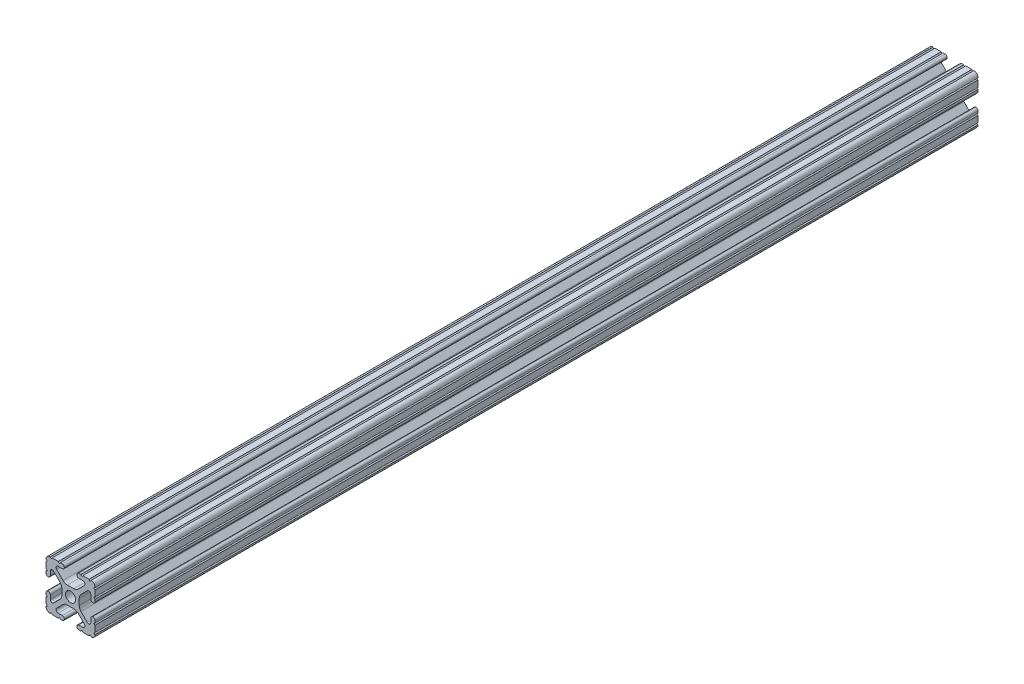
SolidWorks part; units mm, degrees
ref_plane "Front Plane" through (0, 0, 0) normal (0, 0, 1) x (1, 0, 0)
ref_plane "Top Plane" through (0, 0, 0) normal (0, 1, 0) x (1, 0, 0)
ref_plane "Right Plane" through (0, 0, 0) normal (1, 0, 0) x (0, 0, -1)
sketch "Sketch1" plane through (0, 0, 0) normal (0, 0, 1) x (1, 0, 0)
  line L0 (-7.207, 8.7244) -> (-3.8983, 5.4232)
  line L1 (-4.2875, 10.4902) -> (-6.4768, 10.4902)
  line L2 (-3.2385, 11.651) -> (-3.2385, 11.5392)
  line L3 (-5.3171, 12.7) -> (-4.2875, 12.7)
  line L4 (0, 13.4005) -> (0, -14.8534) construction
  line L5 (12.7, 0) -> (-13.9989, 0) construction
  line L6 (-9.5504, 12.7) -> (-6.3331, 12.7)
  line L7 (-12.7, 6.3331) -> (-12.7, 9.5504)
  line L8 (-12.7, 4.2875) -> (-12.7, 5.3171)
  line L9 (-11.5392, 3.2385) -> (-11.651, 3.2385)
  line L10 (-10.4902, 6.4021) -> (-10.4902, 4.2875)
  line L11 (-5.441, 3.8408) -> (-8.7371, 7.1294)
  line L12 (-4.5085, -1.5932) -> (-4.5085, 1.5932)
  line L13 (-1.7093, -4.4958) -> (1.7093, -4.4958)
  line L14 (3.9523, -5.4237) -> (7.1797, -8.6452)
  line L15 (6.4164, -10.4902) -> (4.2875, -10.4902)
  line L16 (3.2385, -11.5392) -> (3.2385, -11.651)
  line L17 (4.2875, -12.7) -> (5.3171, -12.7)
  line L18 (6.3331, -12.7) -> (9.5504, -12.7)
  line L19 (12.7, -9.5504) -> (12.7, -6.3331)
  line L20 (12.7, -5.3171) -> (12.7, -4.2875)
  line L21 (11.651, -3.2385) -> (11.5392, -3.2385)
  line L22 (10.4902, -4.2875) -> (10.4902, -6.4021)
  line L23 (8.7371, -7.1294) -> (5.441, -3.8408)
  line L24 (4.5085, -1.5932) -> (4.5085, 1.5932)
  line L25 (5.441, 3.8408) -> (8.7371, 7.1294)
  line L26 (10.4902, 6.4021) -> (10.4902, 4.2875)
  line L27 (11.5392, 3.2385) -> (11.651, 3.2385)
  line L28 (12.7, 4.2875) -> (12.7, 5.3171)
  line L29 (12.7, 6.3331) -> (12.7, 9.5504)
  line L30 (9.5504, 12.7) -> (6.3331, 12.7)
  line L31 (5.3171, 12.7) -> (4.2875, 12.7)
  line L32 (3.2385, 11.651) -> (3.2385, 11.5392)
  line L33 (4.2875, 10.4902) -> (6.4768, 10.4902)
  line L34 (7.207, 8.7244) -> (3.8983, 5.4232)
  line L35 (1.6558, 4.4958) -> (-1.6558, 4.4958)
  line L36 (-8.7371, -7.1294) -> (-5.441, -3.8408)
  line L37 (-10.4902, -4.2875) -> (-10.4902, -6.4021)
  line L38 (-11.651, -3.2385) -> (-11.5392, -3.2385)
  line L39 (-12.7, -5.3171) -> (-12.7, -4.2875)
  line L40 (-12.7, -9.5504) -> (-12.7, -6.3331)
  line L41 (-6.3331, -12.7) -> (-9.5504, -12.7)
  line L42 (-4.2875, -12.7) -> (-5.3171, -12.7)
  line L43 (-3.2385, -11.5392) -> (-3.2385, -11.651)
  line L44 (-6.4164, -10.4902) -> (-4.2875, -10.4902)
  line L45 (-3.9523, -5.4237) -> (-7.1797, -8.6452)
  arc A0 (-7.207, 8.7244) -> (-6.4768, 10.4902) centre (-6.4768, 9.4563) cw
  arc A1 (-3.2385, 11.5392) -> (-4.2875, 10.4902) centre (-4.2875, 11.5392) cw
  arc A2 (-4.2875, 12.7) -> (-3.2385, 11.651) centre (-4.2875, 11.651) cw
  arc A3 (-5.3171, 12.7) -> (-6.3331, 12.7) centre (-5.8251, 12.7) cw
  arc A4 (-9.5504, 12.7) -> (-10.5664, 12.6998) centre (-10.0584, 12.7) cw
  arc A5 (-12.6998, 10.5664) -> (-10.5664, 12.6998) centre (-10.5918, 10.5918) cw
  arc A6 (-12.6998, 10.5664) -> (-12.7, 9.5504) centre (-12.7, 10.0584) cw
  arc A7 (-12.7, 6.3331) -> (-12.7, 5.3171) centre (-12.7, 5.8251) cw
  arc A8 (-11.651, 3.2385) -> (-12.7, 4.2875) centre (-11.651, 4.2875) cw
  arc A9 (-10.4902, 4.2875) -> (-11.5392, 3.2385) centre (-11.5392, 4.2875) cw
  circle A10 centre (0, 0) radius 2.6035
  arc A11 (-10.4902, 6.4021) -> (-8.7371, 7.1294) centre (-9.4628, 6.4021) cw
  arc A12 (-5.441, 3.8408) -> (-4.5085, 1.5932) centre (-7.6835, 1.5932) cw
  arc A13 (-4.5085, -1.5932) -> (-5.441, -3.8408) centre (-7.6835, -1.5932) cw
  arc A14 (-8.7371, -7.1294) -> (-10.4902, -6.4021) centre (-9.4628, -6.4021) cw
  arc A15 (-1.7093, -4.4958) -> (-3.9523, -5.4237) centre (-1.7093, -7.6708) ccw
  arc A16 (3.9523, -5.4237) -> (1.7093, -4.4958) centre (1.7093, -7.6708) ccw
  arc A17 (6.4164, -10.4902) -> (7.1797, -8.6452) centre (6.4164, -9.4098) ccw
  arc A18 (4.2875, -10.4902) -> (3.2385, -11.5392) centre (4.2875, -11.5392) ccw
  arc A19 (3.2385, -11.651) -> (4.2875, -12.7) centre (4.2875, -11.651) ccw
  arc A20 (6.3331, -12.7) -> (5.3171, -12.7) centre (5.8251, -12.7) ccw
  arc A21 (10.5664, -12.6998) -> (9.5504, -12.7) centre (10.0584, -12.7) ccw
  arc A22 (10.5664, -12.6998) -> (12.6998, -10.5664) centre (10.5918, -10.5918) ccw
  arc A23 (12.7, -9.5504) -> (12.6998, -10.5664) centre (12.7, -10.0584) ccw
  arc A24 (12.7, -5.3171) -> (12.7, -6.3331) centre (12.7, -5.8251) ccw
  arc A25 (12.7, -4.2875) -> (11.651, -3.2385) centre (11.651, -4.2875) ccw
  arc A26 (11.5392, -3.2385) -> (10.4902, -4.2875) centre (11.5392, -4.2875) ccw
  arc A27 (8.7371, -7.1294) -> (10.4902, -6.4021) centre (9.4628, -6.4021) ccw
  arc A28 (4.5085, -1.5932) -> (5.441, -3.8408) centre (7.6835, -1.5932) ccw
  arc A29 (5.441, 3.8408) -> (4.5085, 1.5932) centre (7.6835, 1.5932) ccw
  arc A30 (10.4902, 6.4021) -> (8.7371, 7.1294) centre (9.4628, 6.4021) ccw
  arc A31 (10.4902, 4.2875) -> (11.5392, 3.2385) centre (11.5392, 4.2875) ccw
  arc A32 (11.651, 3.2385) -> (12.7, 4.2875) centre (11.651, 4.2875) ccw
  arc A33 (12.7, 6.3331) -> (12.7, 5.3171) centre (12.7, 5.8251) ccw
  arc A34 (12.6998, 10.5664) -> (12.7, 9.5504) centre (12.7, 10.0584) ccw
  arc A35 (12.6998, 10.5664) -> (10.5664, 12.6998) centre (10.5918, 10.5918) ccw
  arc A36 (9.5504, 12.7) -> (10.5664, 12.6998) centre (10.0584, 12.7) ccw
  arc A37 (5.3171, 12.7) -> (6.3331, 12.7) centre (5.8251, 12.7) ccw
  arc A38 (4.2875, 12.7) -> (3.2385, 11.651) centre (4.2875, 11.651) ccw
  arc A39 (3.2385, 11.5392) -> (4.2875, 10.4902) centre (4.2875, 11.5392) ccw
  arc A40 (7.207, 8.7244) -> (6.4768, 10.4902) centre (6.4768, 9.4563) ccw
  arc A41 (1.6558, 4.4958) -> (3.8983, 5.4232) centre (1.6558, 7.6708) ccw
  arc A42 (-1.6558, 4.4958) -> (-3.8983, 5.4232) centre (-1.6558, 7.6708) cw
  arc A43 (-11.5392, -3.2385) -> (-10.4902, -4.2875) centre (-11.5392, -4.2875) cw
  arc A44 (-12.7, -4.2875) -> (-11.651, -3.2385) centre (-11.651, -4.2875) cw
  arc A45 (-12.7, -5.3171) -> (-12.7, -6.3331) centre (-12.7, -5.8251) cw
  arc A46 (-12.7, -9.5504) -> (-12.6998, -10.5664) centre (-12.7, -10.0584) cw
  arc A47 (-10.5664, -12.6998) -> (-12.6998, -10.5664) centre (-10.5918, -10.5918) cw
  arc A48 (-10.5664, -12.6998) -> (-9.5504, -12.7) centre (-10.0584, -12.7) cw
  arc A49 (-6.3331, -12.7) -> (-5.3171, -12.7) centre (-5.8251, -12.7) cw
  arc A50 (-3.2385, -11.651) -> (-4.2875, -12.7) centre (-4.2875, -11.651) cw
  arc A51 (-4.2875, -10.4902) -> (-3.2385, -11.5392) centre (-4.2875, -11.5392) cw
  arc A52 (-6.4164, -10.4902) -> (-7.1797, -8.6452) centre (-6.4164, -9.4098) cw
  dimension "D1" = 5.207
  dimension "D9" = 14.859
  dimension "D2" = 25.4
  dimension "D3" = 12.7
  dimension "D4" = 6.477
  dimension "D5" = 8.2042
  dimension "D6" = 9.017
  dimension "D8" = 2.2098
  dimension "D10" = 2.2098
extrude "Extrude1" add sketch "Sketch1" against normal blind 457.2
